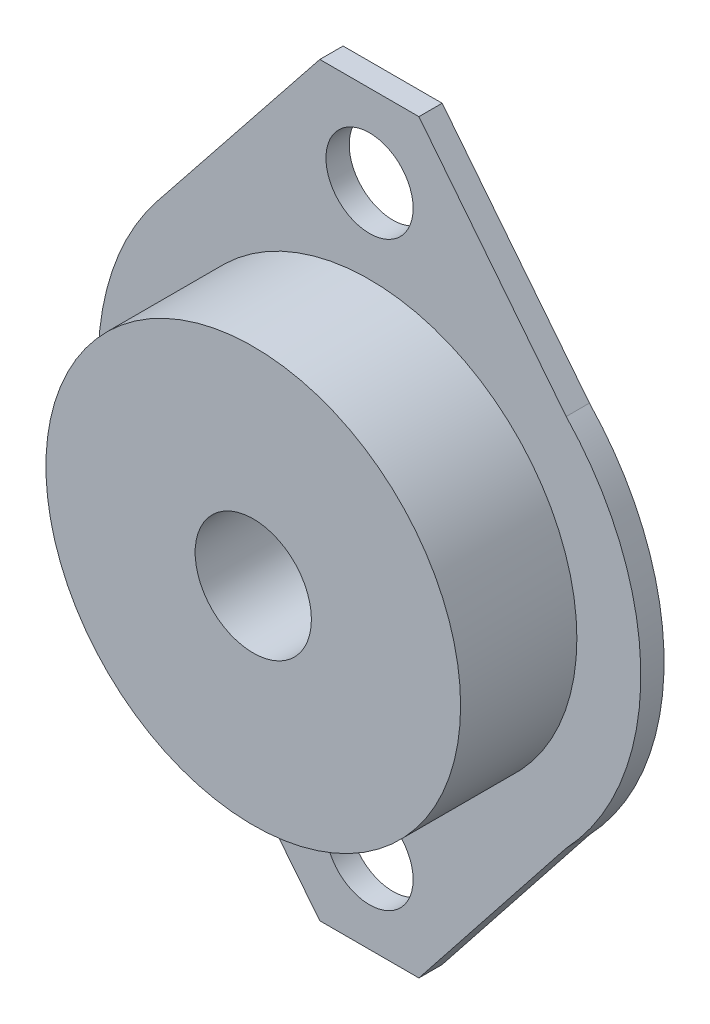
SolidWorks part; units mm, degrees
ref_plane "正面" through (0, 0, 0) normal (0, 0, 1) x (1, 0, 0)
ref_plane "平面" through (0, 0, 0) normal (0, 1, 0) x (1, 0, 0)
ref_plane "右側面" through (0, 0, 0) normal (1, 0, 0) x (0, 0, -1)
sketch "ｽｹｯﾁ1" plane through (0, 0, 0) normal (0, 0, 1) x (1, 0, 0)
  line L0 (-10.9494, 8.7242) -> (0, 22.4663)
  line L1 (0, 22.4663) -> (10.1481, 9.6444)
  line L2 (-10.9494, -8.7242) -> (0, -22.4663)
  line L3 (0, -22.4663) -> (10.1481, -9.6444)
  arc A0 (10.1481, -9.6444) -> (10.1481, 9.6444) centre (0, 0) ccw
  circle A1 centre (0, 15) radius 2.25
  circle A2 centre (0, -15) radius 2.25
  arc A3 (-10.9494, 8.7242) -> (-10.9494, -8.7242) centre (0, 0) ccw
  circle A4 centre (0, 0) radius 3
  dimension "D1" = 28
  dimension "D2" = 4.5
  dimension "D3" = 4.5
  dimension "D4" = 15
  dimension "D6" = 6
  dimension "D5" = 15
extrude "ﾎﾞｽ - 押し出し1" add sketch "ｽｹｯﾁ1" along normal blind 1.2
sketch "ｽｹｯﾁ2" plane through (0, 0, 1.2) normal (0, 0, 1) x (1, 0, 0)
  circle A0 centre (0, 0) radius 10.7
  circle A1 centre (0, 0) radius 3
  dimension "D1" = 21.4
extrude "ﾎﾞｽ - 押し出し2" add sketch "ｽｹｯﾁ2" along normal blind 6
sketch "ｽｹｯﾁ3" plane through (0, 0, 1.2) normal (0, 0, 1) x (1, 0, 0)
  line L0 (-2.565, 19.2471) -> (2.548, 19.2471)
  line L1 (0, 22.4663) -> (-10.9494, 8.7242) construction
  line L2 (10.1481, 9.6444) -> (0, 22.4663) construction
  line L3 (-2.565, -19.2471) -> (2.548, -19.2471)
  line L4 (-10.9494, -8.7242) -> (0, -22.4663) construction
  line L5 (0, -22.4663) -> (10.1481, -9.6444) construction
  line L6 (2.548, -19.2471) -> (0, -22.4663)
  line L7 (0, -22.4663) -> (-2.565, -19.2471)
  line L8 (-2.565, 19.2471) -> (0, 22.4663)
  line L9 (0, 22.4663) -> (2.548, 19.2471)
extrude "ｶｯﾄ - 押し出し1" cut sketch "ｽｹｯﾁ3" against normal blind 6
